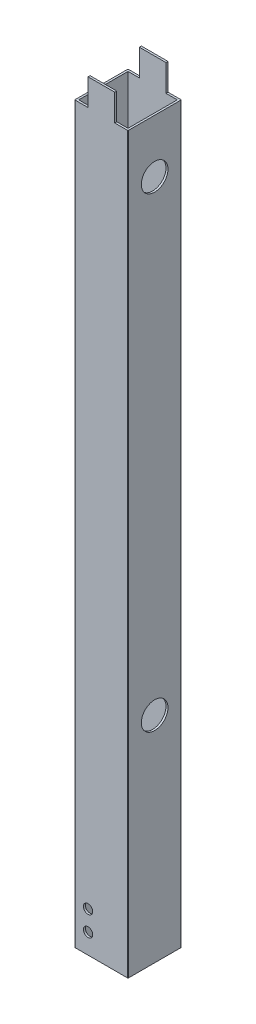
SolidWorks part; units mm, degrees
ref_plane "Front Plane" through (0, 0, 0) normal (0, 0, 1) x (1, 0, 0)
ref_plane "Top Plane" through (0, 0, 0) normal (0, 1, 0) x (1, 0, 0)
ref_plane "Right Plane" through (0, 0, 0) normal (1, 0, 0) x (0, 0, -1)
sketch "Sketch1" plane through (0, 0, 0) normal (0, 1, 0) x (1, 0, 0)
  line L0 (1.5, 1.5) -> (38.5, 1.5)
  line L1 (0.5, 0) -> (39.5, 0)
  line L2 (0, 0.5) -> (0, 39.5)
  line L3 (0.5, 40) -> (39.5, 40)
  line L4 (40, 0.5) -> (40, 39.5)
  line L5 (38.5, 1.5) -> (38.5, 38.5)
  line L6 (1.5, 38.5) -> (38.5, 38.5)
  line L7 (1.5, 1.5) -> (1.5, 38.5)
  arc A0 (39.5, 0) -> (40, 0.5) centre (39.5, 0.5) ccw
  arc A1 (0.5, 0) -> (0, 0.5) centre (0.5, 0.5) cw
  arc A2 (0, 39.5) -> (0.5, 40) centre (0.5, 39.5) cw
  arc A3 (39.5, 40) -> (40, 39.5) centre (39.5, 39.5) cw
  arc A4 (38.5, 1.5) -> (38.5, 1.5) centre (38.5, 1.5) ccw
  arc A5 (38.5, 38.5) -> (38.5, 38.5) centre (38.5, 38.5) cw
  arc A6 (1.5, 38.5) -> (1.5, 38.5) centre (1.5, 38.5) cw
  arc A7 (1.5, 1.5) -> (1.5, 1.5) centre (1.5, 1.5) cw
  point P9 (0, 0)
  dimension "D3" = 0.5
  dimension "D1" = 40
  dimension "D2" = 40
  dimension "D4" = 1.5
extrude "Boss-Extrude1" add sketch "Sketch1" along normal blind 571
sketch "Sketch2" plane through (0, 0, -40) normal (0, 0, 1) x (1, 0, 0)
  line L0 (0.5, 571) -> (39.5, 571) construction
  line L11 (30, 571) -> (40, 571)
  line L12 (30, 571) -> (30, 551)
  line L13 (30, 551) -> (40, 551)
  line L14 (40, 571) -> (40, 551)
  line L15 (40, 571) -> (40, 0) construction
  line L16 (20, 571) -> (20, 1571.1839) construction
  line L17 (0, 571) -> (0, 551)
  line L18 (10, 551) -> (0, 551)
  line L19 (10, 571) -> (10, 551)
  line L20 (10, 571) -> (0, 571)
  dimension "D1" = 20
  dimension "D2" = 10
extrude "Cut-Extrude1" cut sketch "Sketch2" along normal blind 40
sketch "Sketch3" plane through (40, 0, 0) normal (1, 0, 0) x (0, 0, -1)
  line L0 (40, 551) -> (40, 0) construction
  line L5 (19, 468.5) -> (40, 468.5)
  line L7 (19, 468.5) -> (19, 466.5)
  line L17 (19, 466.5) -> (40, 466.5)
  line L22 (40, 468.5) -> (40, 466.5)
  line L23 (0.5, 551) -> (39.5, 551) construction
  line L24 (40, 448.5) -> (21.8195, 448.5) construction
  line L25 (40, 428.5) -> (40, 430.5)
  line L26 (19, 430.5) -> (40, 430.5)
  line L27 (19, 428.5) -> (19, 430.5)
  line L28 (19, 428.5) -> (40, 428.5)
  dimension "D1" = 2
  dimension "D2" = 21
  dimension "D3" = 82.5
  dimension "D4" = 20
extrude "Cut-Extrude2" cut sketch "Sketch3" against normal blind 20 from offset 20 offset against normal yes
sketch "Sketch4" plane through (0, 0, -40) normal (0, 0, -1) x (-1, 0, 0)
  line L55 (-20, 0) -> (-20, 25.0728) construction
  line L62 (-39.5, 0) -> (-0.5, 0) construction
  line L63 (0, 50.5059) -> (-4.7733, 47.75) construction
  line L64 (0, 73.5999) -> (0.775, 74.0473) construction
  line L65 (-3, 71.8678) -> (0, 73.5999) construction
  line L66 (-4.7733, 47.75) -> (-7.2733, 52.0801)
  line L67 (-3, 48.7738) -> (-4.7733, 47.75)
  line L68 (0, 48.7738) -> (0, 56.2794)
  line L69 (-3, 48.7738) -> (0, 48.7738)
  line L70 (-3, 54.5473) -> (-7.2733, 52.0801)
  line L71 (-3, 56.2794) -> (-3, 54.5473)
  line L72 (0, 56.2794) -> (-3, 56.2794)
  line L73 (0, 66.0943) -> (0, 73.5999)
  line L74 (-3, 66.0943) -> (0, 66.0943)
  line L75 (-11.8403, 60.9904) -> (-3, 66.0943)
  line L76 (-14.3403, 65.3205) -> (-11.8403, 60.9904)
  line L77 (-3, 71.8678) -> (-14.3403, 65.3205)
  line L78 (-3, 73.5999) -> (-3, 71.8678)
  line L79 (0, 73.5999) -> (-3, 73.5999)
extrude "Cut-Extrude3" cut sketch "Sketch4" against normal blind 20
sketch "Sketch5" plane through (0, 0, 0) normal (0, 0, 1) x (1, 0, 0)
  line L0 (0.5, 0) -> (39.5, 0) construction
  line L1 (40, 551) -> (40, 0) construction
  circle A0 centre (10, 15) radius 3.5
  circle A1 centre (10, 30) radius 3.5
  dimension "D1" = 15
  dimension "D2" = 15
  dimension "D3" = 7
  dimension "D4" = 30
extrude "Cut-Extrude4" cut sketch "Sketch5" against normal blind 10
sketch "Sketch6" plane through (0, 0, 0) normal (-1, 0, 0) x (0, 0, 1)
  line L0 (-0.5, 551) -> (-39.5, 551) construction
  circle A0 centre (-20, 511) radius 10
  circle A1 centre (-20, 161) radius 10
  point P4 (0, 0)
  point P5 (-20, 551)
  dimension "D1" = 40
  dimension "D2" = 20
  dimension "D3" = 350
extrude "Cut-Extrude5" cut sketch "Sketch6" against normal through all
